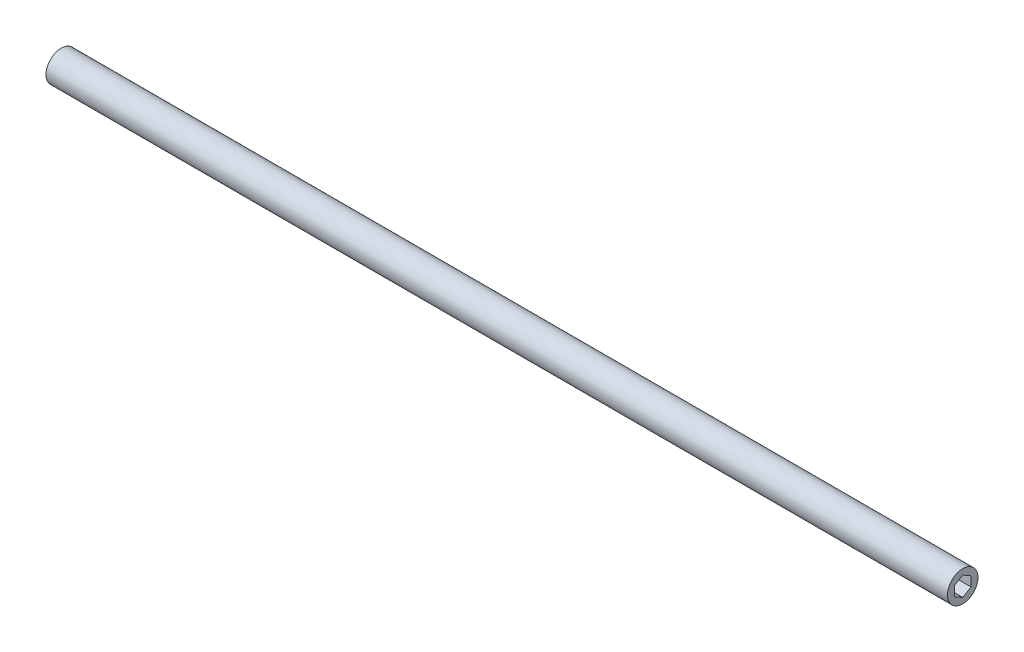
SolidWorks part; units mm, degrees
ref_plane "Front" through (0, 0, 0) normal (0, 0, 1) x (1, 0, 0)
ref_plane "Top" through (0, 0, 0) normal (0, 1, 0) x (1, 0, 0)
ref_plane "Right" through (0, 0, 0) normal (1, 0, 0) x (0, 0, -1)
sketch "Sketch1" plane through (0, 0, 0) normal (1, 0, 0) x (0, 0, -1)
  line L1 (0, 7.3323) -> (-6.35, 3.6662)
  line L2 (-6.35, 3.6662) -> (-6.35, -3.6662)
  line L3 (-6.35, -3.6662) -> (0, -7.3323)
  line L4 (0, -7.3323) -> (6.35, -3.6662)
  line L5 (6.35, -3.6662) -> (6.35, 3.6662)
  line L6 (6.35, 3.6662) -> (0, 7.3323)
  circle A0 centre (0, 0) radius 11.557
  circle A1 centre (0, 0) radius 6.35 construction
  dimension "D2" = 23.114
  dimension "D1" = 12.7
extrude "Boss-Extrude1" add sketch "Sketch1" along normal blind 682.625
